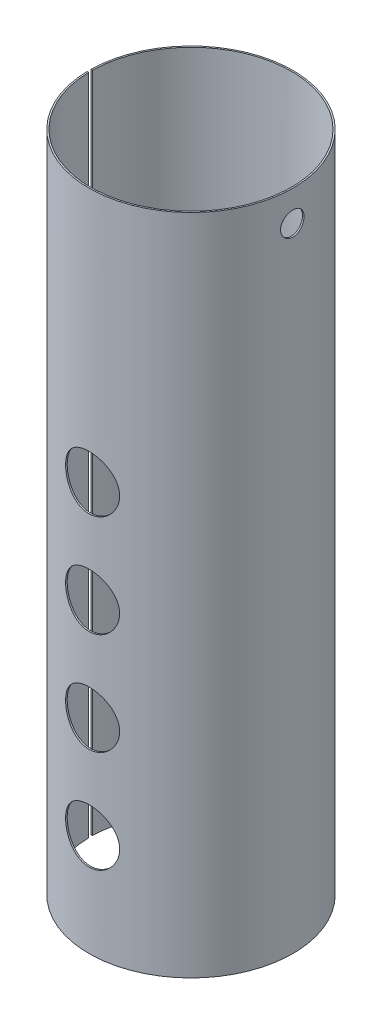
SolidWorks part; units mm, degrees
material "Kupfer"
ref_plane "Ebene vorne" through (0, 0, 0) normal (0, 0, 1) x (1, 0, 0)
ref_plane "Ebene oben" through (0, 0, 0) normal (0, 1, 0) x (1, 0, 0)
ref_plane "Ebene rechts" through (0, 0, 0) normal (1, 0, 0) x (0, 0, -1)
sketch "Skizze1" plane through (0, 0, 0) normal (0, 0, 1) x (1, 0, 0)
  line L0 (0, 750) -> (0, 0) construction
  line L1 (-100, 0) -> (100, 0) construction
  line L2 (-100, 0) -> (-100, 20)
  line L3 (-100, 30) -> (-100, 650)
  line L4 (-100, 30) -> (-100, 20)
  arc A0 (-100, 20) -> (-100, 30) centre (-100, 25) cw construction
  dimension "D4" = 5
  dimension "D1" = 750
  dimension "D2" = 200
  dimension "D3" = 650
  dimension "D5" = 20
revolve "Rotation-Dünn1" add sketch "Skizze1" angle 360 about L0
sketch "Skizze2" plane through (0, 0, 0) normal (0, 0, 1) x (1, 0, 0)
  line L0 (0, 0) -> (0, 650) construction
  line L1 (98.5, 650) -> (-98.5, 650) construction
  circle A0 centre (0, 100) radius 26.5
  circle A1 centre (0, 200) radius 26.5
  circle A2 centre (0, 300) radius 26.5
  circle A3 centre (0, 400) radius 26.5
  dimension "D1" = 53
  dimension "D2" = 100
  dimension "D3" = 100
  dimension "D4" = 100
  dimension "D5" = 100
extrude "Schnitt-Linear austragen1" cut sketch "Skizze2" along normal up to next
sketch "Skizze3" plane through (0, 0, 0) normal (1, 0, 0) x (0, 0, -1)
  line L0 (100, 650) -> (-100, 650) construction
  circle A0 centre (0, 620) radius 11.5
  dimension "D1" = 23
  dimension "D2" = 30
extrude "Schnitt-Linear austragen2" cut sketch "Skizze3" along normal up to next
ref_plane "Ebene1" through (-100, 0, 0) normal (-1, 0, 0) x (0, 0, 1)
sketch "Skizze4" plane through (0, 0, 0) normal (0, 0, 1) x (1, 0, 0)
  circle A0 centre (0, 400) radius 14
  circle A1 centre (0, 300) radius 14
  circle A2 centre (0, 200) radius 14
  circle A3 centre (0, 100) radius 14
  dimension "D1" = 28
extrude "Schnitt-Linear austragen3" cut sketch "Skizze4" against normal up to next
sketch "Skizze5" plane through (0, 0, 0) normal (0, 1, 0) x (1, 0, 0)
  line L0 (0, 0) -> (-98.5, 0) construction
  line L1 (-26.5, 0) -> (26.5, 0) construction
  line L2 (-101.0191, 2) -> (0, 0)
  line L3 (0, 0) -> (-101.0191, -2)
  line L4 (-101.0191, 2) -> (-101.0191, -2)
  line L5 (-101.0191, 2) -> (-101.0191, -2)
  circle A0 centre (0, 0) radius 98.5 construction
  dimension "D1" = 2
  dimension "D2" = 2
extrude "Schnitt-Linear austragen4" cut sketch "Skizze5" along normal through all
